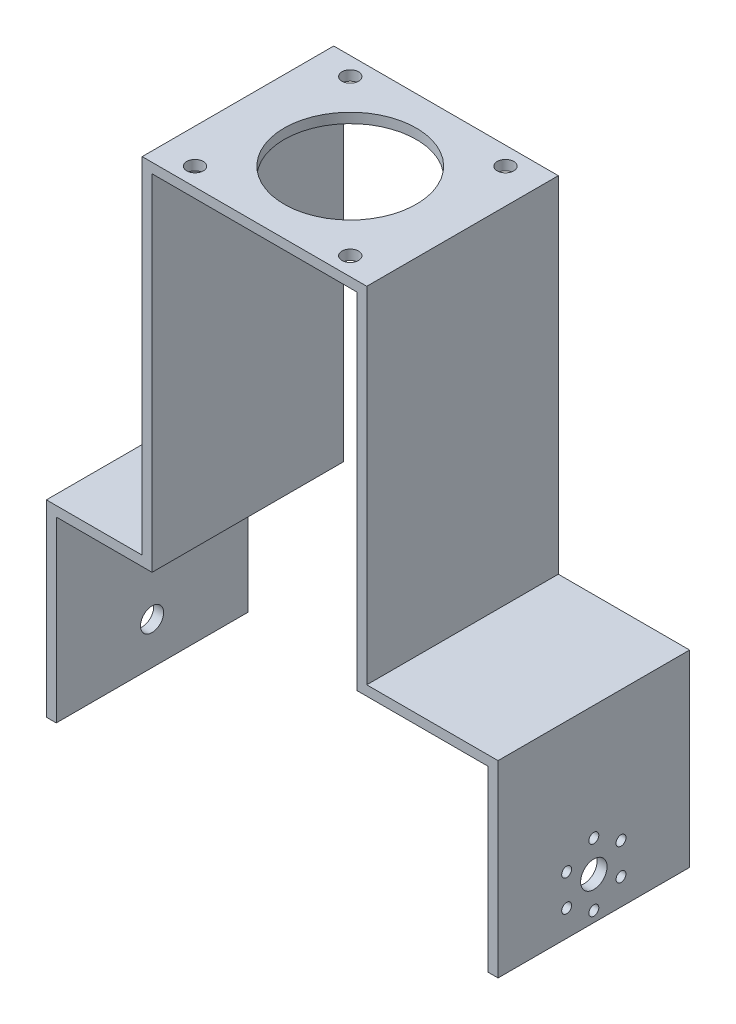
SolidWorks part; units mm, degrees
material "1060 Alloy"
ref_plane "Front Plane" through (0, 0, 0) normal (0, 0, 1) x (1, 0, 0)
ref_plane "Top Plane" through (0, 0, 0) normal (0, 1, 0) x (1, 0, 0)
ref_plane "Right Plane" through (0, 0, 0) normal (1, 0, 0) x (0, 0, -1)
sketch "Sketch2" plane through (0, 0, 0) normal (0, 0, 1) x (1, 0, 0)
  line L0 (2, 51.8967) -> (36, 51.8967)
  line L1 (36, 51.8967) -> (36, -52.6033)
  line L2 (36, -52.6033) -> (75.75, -52.6033)
  line L3 (75.75, -52.6033) -> (75.75, -109.6033)
  line L4 (2, 51.8967) -> (-32, 51.8967)
  line L5 (-32, 51.8967) -> (-32, -52.6033)
  line L6 (-32, -52.6033) -> (-61, -52.6033)
  line L7 (-61, -52.6033) -> (-61, -109.6033)
  line L8 (-58, -55.6033) -> (-58, -109.6033)
  line L9 (-29, -55.6033) -> (-58, -55.6033)
  line L10 (-29, 48.8967) -> (-29, -55.6033)
  line L11 (2, 48.8967) -> (-29, 48.8967)
  line L12 (2, 48.8967) -> (33, 48.8967)
  line L13 (33, 48.8967) -> (33, -55.6033)
  line L14 (33, -55.6033) -> (72.75, -55.6033)
  line L15 (72.75, -55.6033) -> (72.75, -109.6033)
  line L16 (-61, -109.6033) -> (-58, -109.6033)
  line L17 (72.75, -109.6033) -> (75.75, -109.6033)
  dimension "D1" = 34
  dimension "D2" = 104.5
  dimension "D3" = 39.75
  dimension "D4" = 57
  dimension "D5" = 34
  dimension "D6" = 29
  dimension "D7" = 3
extrude "Boss-Extrude1" add sketch "Sketch2" along normal blind 58
sketch "Sketch5" plane through (-61, 0, 0) normal (-1, 0, 0) x (0, 0, 1)
  line L0 (0, -109.6033) -> (0, -96.9033) construction
  line L1 (0, -52.6033) -> (0, -109.6033) construction
  line L2 (0, -96.9033) -> (29, -96.9033) construction
  circle A0 centre (29, -96.9033) radius 3.5
  dimension "D2" = 7
  dimension "D1" = 12.7
extrude "Cut-Extrude3" cut sketch "Sketch5" against normal blind 58
sketch "Sketch7" plane through (75.75, 0, 0) normal (1, 0, 0) x (0, 0, -1)
  line L0 (-29, -109.6033) -> (-29, -96.9024) construction
  line L1 (-58, -109.6033) -> (0, -109.6033) construction
sketch "Sketch8" plane through (75.75, -106.8485, 47.0728) normal (1, 0, 0) x (0, 0, -1)
  line L0 (18.0728, 9.946) -> (27.5728, 9.946) construction
  circle A0 centre (18.0728, 9.946) radius 9.5
  dimension "D1" = 19
sketch "Sketch15" plane through (75.75, 0, 0) normal (1, 0, 0) x (0, 0, -1)
  circle A0 centre (-29, -96.9024) radius 4
  dimension "D1" = 8
extrude "Cut-Extrude4" cut sketch "Sketch15" against normal blind 10
sketch "Sketch16" plane through (75.75, 0, 0) normal (1, 0, 0) x (0, 0, -1)
  circle A0 centre (-29, -87.4024) radius 1.5
  circle A1 centre (-29, -96.9024) radius 9.5 construction
  circle A2 centre (-20.7728, -92.1524) radius 1.5
  circle A3 centre (-20.7728, -101.6524) radius 1.5
  circle A4 centre (-29, -106.4024) radius 1.5
  circle A5 centre (-37.2272, -101.6524) radius 1.5
  circle A6 centre (-37.2272, -92.1524) radius 1.5
  point P17 (-29, -96.9024)
  dimension "D1" = 3
  dimension "D2" = 6
extrude "Cut-Extrude5" cut sketch "Sketch16" against normal blind 10
sketch "Sketch17" plane through (0, 51.8967, 0) normal (0, 1, 0) x (1, 0, 0)
  line L0 (-25.2689, 0) -> (-25.2689, -5.5) construction
  line L1 (36, 0) -> (-32, 0) construction
  line L2 (-32, -5.5) -> (-21.5, -5.5) construction
  line L3 (-32, -58) -> (-32, 0) construction
  line L4 (2, 0) -> (2, -58) construction
  line L5 (36, -58) -> (-32, -58) construction
  line L6 (-32, -29) -> (36, -29) construction
  line L7 (-32, -58) -> (-32, 0) construction
  line L8 (36, -58) -> (36, 0) construction
  circle A0 centre (2, -29) radius 20
  circle A1 centre (-21.5, -5.5) radius 2.5
  circle A2 centre (25.5, -5.5) radius 2.5
  circle A3 centre (25.5, -52.5) radius 2.5
  circle A4 centre (-21.5, -52.5) radius 2.5
  dimension "D3" = 40
  dimension "D4" = 5
  dimension "D1" = 5.5
  dimension "D2" = 10.5
extrude "Cut-Extrude6" cut sketch "Sketch17" against normal blind 10
